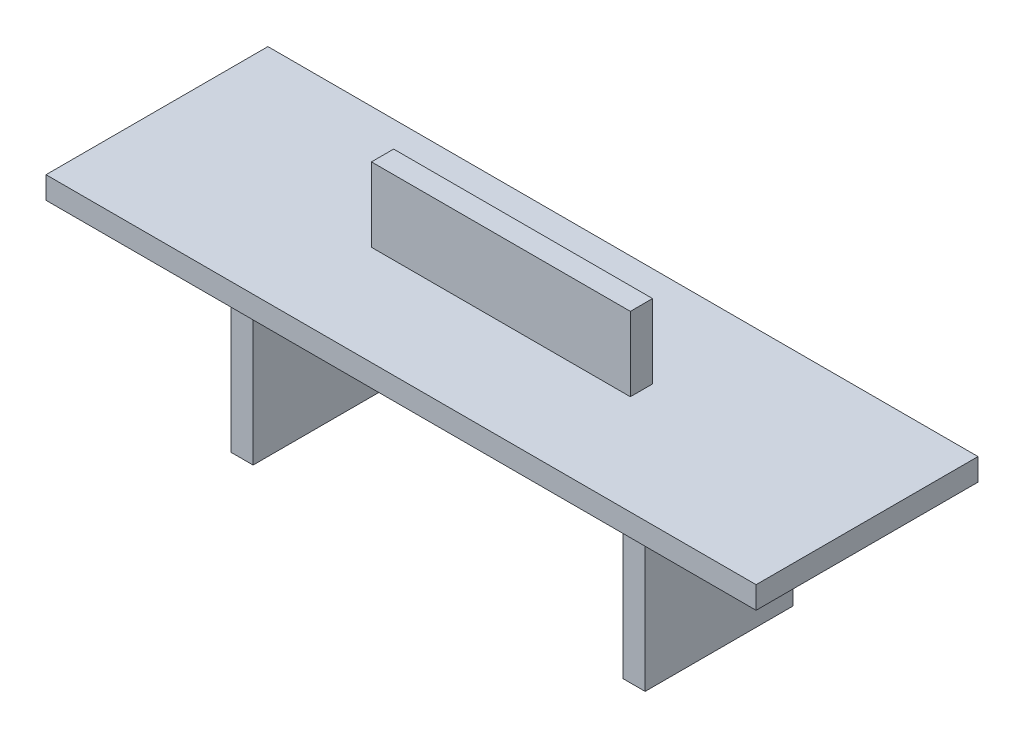
SolidWorks part; units mm, degrees
ref_plane "Front Plane" through (0, 0, 0) normal (0, 0, 1) x (1, 0, 0)
ref_plane "Top Plane" through (0, 0, 0) normal (0, 1, 0) x (1, 0, 0)
ref_plane "Right Plane" through (0, 0, 0) normal (1, 0, 0) x (0, 0, -1)
sketch "Sketch1" plane through (0, 0, 0) normal (0, 0, 1) x (1, 0, 0)
  line L0 (-48, 3) -> (48, 3)
  line L1 (48, 3) -> (48, 0)
  line L2 (48, 0) -> (28, 0)
  line L3 (28, 0) -> (28, -22)
  line L4 (28, -22) -> (25, -22)
  line L5 (25, -22) -> (25, 0)
  line L6 (25, 0) -> (-25, 0)
  line L7 (-25, 0) -> (-25, -22)
  line L8 (-25, -22) -> (-28, -22)
  line L9 (-28, -22) -> (-28, 0)
  line L10 (-28, 0) -> (-48, 0)
  line L11 (-48, 0) -> (-48, 3)
  point P10 (0, 0)
  dimension "D1" = 3
  dimension "D2" = 50
  dimension "D3" = 20
  dimension "D4" = 20
  dimension "D5" = 22
extrude "Boss-Extrude1" add sketch "Sketch1" along normal blind 30
sketch "Sketch2" plane through (-28, 0, 0) normal (-1, 0, 0) x (0, 0, 1)
  line L0 (30, -22) -> (0, -22) construction
  line L1 (0, 0) -> (5, 0)
  line L2 (0, 0) -> (0, -22)
  line L3 (0, -22) -> (5, -22)
  line L4 (5, 0) -> (5, -22)
  line L5 (30, 0) -> (0, 0) construction
  line L6 (25, 0) -> (30, 0)
  line L7 (25, 0) -> (25, -22)
  line L8 (25, -22) -> (30, -22)
  line L9 (30, 0) -> (30, -22)
  dimension "D1" = 5
  dimension "D2" = 5
extrude "Cut-Extrude1" cut sketch "Sketch2" against normal through all
sketch "Sketch3" plane through (0, 3, 0) normal (0, 1, 0) x (1, 0, 0)
  line L0 (0, -15) -> (-48, -15) construction
  line L1 (-17.5, -16.5) -> (17.5, -16.5)
  line L2 (-17.5, -16.5) -> (-17.5, -13.5)
  line L3 (-17.5, -13.5) -> (17.5, -13.5)
  line L4 (17.5, -16.5) -> (17.5, -13.5)
  line L5 (-17.5, -16.5) -> (17.5, -13.5) construction
  line L6 (-17.5, -13.5) -> (17.5, -16.5) construction
  line L7 (-48, -30) -> (-48, 0) construction
  point P0 (0, -15)
  point P9 (0, 0)
  dimension "D1" = 3
  dimension "D2" = 35
extrude "Boss-Extrude2" add sketch "Sketch3" along normal blind 10
